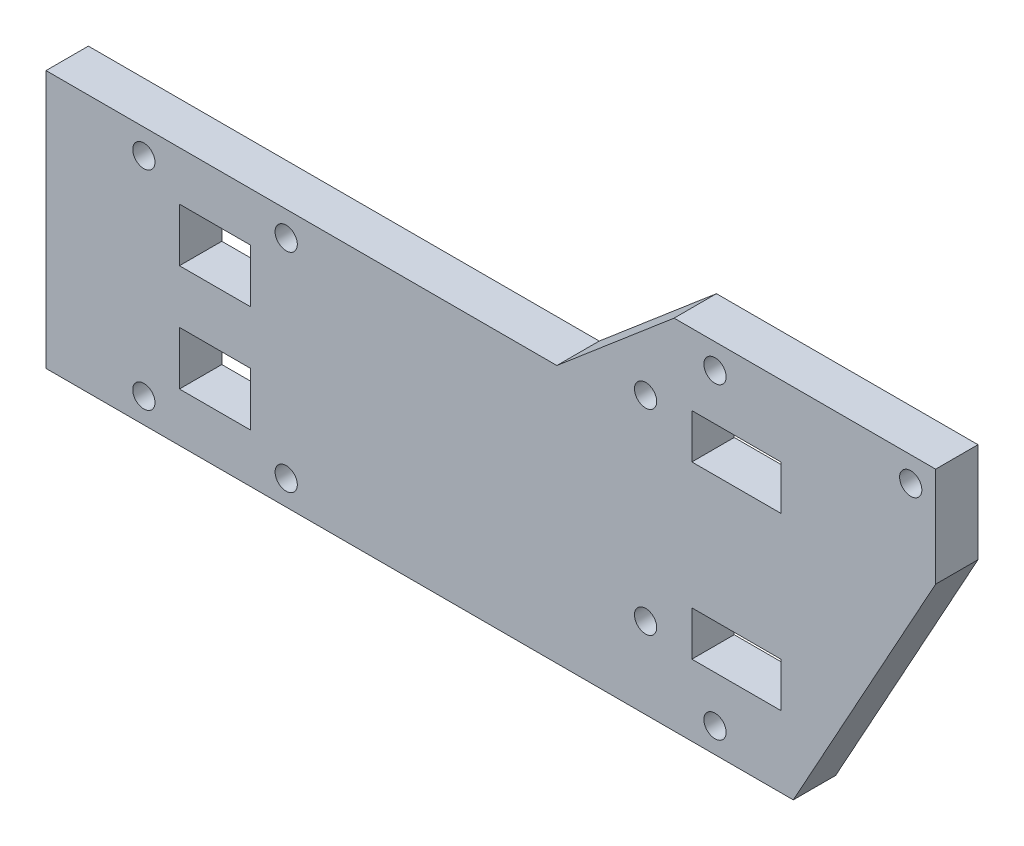
SolidWorks part; units mm, degrees
ref_plane "Front Plane" through (0, 0, 0) normal (0, 0, 1) x (1, 0, 0)
ref_plane "Top Plane" through (0, 0, 0) normal (0, 1, 0) x (1, 0, 0)
ref_plane "Right Plane" through (0, 0, 0) normal (1, 0, 0) x (0, 0, -1)
sketch "Sketch1" plane through (0, 0, 0) normal (0, 0, 1) x (1, 0, 0)
  line L0 (70.6, 40.2) -> (57.4235, 29)
  line L1 (70.6, 40.2) -> (100, 40.2)
  line L2 (100, 40.2) -> (100, 29)
  line L3 (100, 29) -> (84, 0)
  line L4 (84, 0) -> (0, 0)
  line L5 (57.4235, 29) -> (0, 29)
  line L6 (0, 29) -> (0, 0)
  line L7 (64.6, 35.1) -> (70.6, 35.1) construction
  line L8 (70.6, 35.1) -> (70.6, 40.2) construction
  dimension "D1" = 29.4
  dimension "D2" = 100
  dimension "D3" = 29
  dimension "D4" = 40.2
  dimension "D5" = 16
  dimension "D6" = 6
  dimension "D7" = 5.1
extrude "Boss-Extrude1" add sketch "Sketch1" along normal blind 4.7625
sketch "Sketch2" plane through (0, 0, 4.7625) normal (0, 0, 1) x (1, 0, 0)
  line L0 (100, 29) -> (100, 40.2) construction
  line L1 (72.6, 27.2) -> (82.6, 27.2)
  line L2 (72.6, 27.2) -> (72.6, 32.2)
  line L3 (72.6, 32.2) -> (82.6, 32.2)
  line L4 (82.6, 27.2) -> (82.6, 32.2)
  line L5 (72.6, 27.2) -> (82.6, 32.2) construction
  line L6 (72.6, 32.2) -> (82.6, 27.2) construction
  line L7 (100, 40.2) -> (70.6, 40.2) construction
  line L8 (19, 20.5) -> (19, 8.5) construction
  line L9 (72.6, 13) -> (82.6, 13)
  line L10 (72.6, 13) -> (72.6, 8)
  line L11 (72.6, 8) -> (82.6, 8)
  line L12 (82.6, 13) -> (82.6, 8)
  line L13 (72.6, 13) -> (82.6, 8) construction
  line L14 (72.6, 8) -> (82.6, 13) construction
  line L15 (15, 17.5) -> (23, 17.5)
  line L16 (15, 17.5) -> (15, 23.5)
  line L17 (15, 23.5) -> (23, 23.5)
  line L18 (23, 17.5) -> (23, 23.5)
  line L19 (15, 17.5) -> (23, 23.5) construction
  line L20 (15, 23.5) -> (23, 17.5) construction
  line L21 (15, 5.5) -> (23, 5.5)
  line L22 (15, 5.5) -> (15, 11.5)
  line L23 (15, 11.5) -> (23, 11.5)
  line L24 (23, 5.5) -> (23, 11.5)
  line L25 (15, 5.5) -> (23, 11.5) construction
  line L26 (15, 11.5) -> (23, 5.5) construction
  line L27 (0, 29) -> (0, 0) construction
  line L28 (19, 14.5) -> (0, 14.5) construction
  line L29 (0, 0) -> (84, 0) construction
  line L31 (11, 2.8) -> (27, 2.8) construction
  line L32 (11, 2.8) -> (11, 26.2) construction
  line L33 (11, 26.2) -> (27, 26.2) construction
  line L34 (27, 2.8) -> (27, 26.2) construction
  line L35 (11, 2.8) -> (27, 26.2) construction
  line L36 (11, 26.2) -> (27, 2.8) construction
  circle A0 centre (97.2, 37.4) radius 1.25
  circle A1 centre (75.2, 37.4) radius 1.25
  circle A2 centre (67.4, 31.1) radius 1.25
  circle A3 centre (67.4, 9.1) radius 1.25
  circle A4 centre (75.2, 2.8) radius 1.25
  circle A5 centre (11, 26.2) radius 1.25
  circle A6 centre (27, 26.2) radius 1.25
  circle A7 centre (27, 2.8) radius 1.25
  circle A8 centre (11, 2.8) radius 1.25
  point P0 (77.6, 29.7)
  point P9 (77.6, 10.5)
  point P14 (19, 20.5)
  point P19 (19, 8.5)
  dimension "D13" = 2.5
  dimension "D14" = 1.1
  dimension "D1" = 5
  dimension "D2" = 10
  dimension "D3" = 17.4
  dimension "D4" = 8
  dimension "D5" = 14.2
  dimension "D6" = 15
  dimension "D7" = 6
  dimension "D8" = 6
  dimension "D9" = 8
  dimension "D10" = 22
  dimension "D11" = 2.8
  dimension "D12" = 2.8
  dimension "D15" = 5.2
  dimension "D16" = 1.1
  dimension "D17" = 2.8
  dimension "D18" = 16
  dimension "D19" = 2.8
extrude "Cut-Extrude1" cut sketch "Sketch2" against normal through all
sketch "Sketch3" plane through (0, 0, 4.7625) normal (0, 0, 1) x (1, 0, 0)
  line L0 (15, 23.5) -> (23, 23.5) construction
  line L1 (23, 23.5) -> (23, 17.5) construction
  line L2 (23, 17.5) -> (15, 17.5) construction
  line L3 (15, 17.5) -> (15, 23.5) construction
  line L4 (23, 17.5) -> (23, 23.5) construction
  line L5 (15, 17.5) -> (23, 17.5) construction
  line L6 (15, 23.5) -> (15, 17.5) construction
  line L7 (0, 29) -> (0, 0)
  line L8 (0, 0) -> (84, 0)
  line L9 (84, 0) -> (100, 29)
  line L10 (100, 29) -> (100, 40.2)
  line L11 (100, 40.2) -> (70.6, 40.2)
  line L12 (70.6, 40.2) -> (57.4235, 29)
  line L13 (57.4235, 29) -> (0, 29)
  line L14 (0, 29) -> (0, 0)
  line L15 (0, 0) -> (84, 0)
  line L16 (84, 0) -> (100, 29)
  line L17 (100, 29) -> (100, 40.2)
  line L18 (100, 40.2) -> (70.6, 40.2)
  line L19 (70.6, 40.2) -> (57.4235, 29)
  line L20 (57.4235, 29) -> (0, 29)
  line L21 (15, 11.5) -> (23, 11.5) construction
  line L22 (23, 11.5) -> (23, 5.5) construction
  line L23 (23, 5.5) -> (15, 5.5) construction
  line L24 (15, 5.5) -> (15, 11.5) construction
  line L25 (72.6, 13) -> (82.6, 13) construction
  line L26 (82.6, 13) -> (82.6, 8) construction
  line L27 (82.6, 8) -> (72.6, 8) construction
  line L28 (72.6, 8) -> (72.6, 13) construction
  line L29 (72.6, 32.2) -> (82.6, 32.2) construction
  line L30 (82.6, 32.2) -> (82.6, 27.2) construction
  line L31 (82.6, 27.2) -> (72.6, 27.2) construction
  line L32 (72.6, 27.2) -> (72.6, 32.2) construction
  line L33 (15, 23.5) -> (23, 23.5)
  line L34 (23, 23.5) -> (23, 17.5)
  line L35 (23, 17.5) -> (15, 17.5)
  line L36 (15, 17.5) -> (15, 23.5)
  line L37 (23, 17.5) -> (23, 23.5)
  line L38 (15, 17.5) -> (23, 17.5)
  line L39 (15, 23.5) -> (15, 17.5)
  line L40 (15, 11.5) -> (23, 11.5)
  line L41 (23, 11.5) -> (23, 5.5)
  line L42 (23, 5.5) -> (15, 5.5)
  line L43 (15, 5.5) -> (15, 11.5)
  line L44 (72.6, 13) -> (82.6, 13)
  line L45 (82.6, 13) -> (82.6, 8)
  line L46 (82.6, 8) -> (72.6, 8)
  line L47 (72.6, 8) -> (72.6, 13)
  line L48 (72.6, 32.2) -> (82.6, 32.2)
  line L49 (82.6, 32.2) -> (82.6, 27.2)
  line L50 (82.6, 27.2) -> (72.6, 27.2)
  line L51 (72.6, 27.2) -> (72.6, 32.2)
  circle A0 centre (11, 26.2) radius 1.25 construction
  circle A1 centre (27, 26.2) radius 1.25 construction
  circle A2 centre (11, 2.8) radius 1.25 construction
  circle A3 centre (27, 2.8) radius 1.25 construction
  circle A4 centre (67.4, 31.1) radius 1.25 construction
  circle A5 centre (75.2, 37.4) radius 1.25 construction
  circle A6 centre (97.2, 37.4) radius 1.25 construction
  circle A7 centre (67.4, 9.1) radius 1.25 construction
  circle A8 centre (75.2, 2.8) radius 1.25 construction
  circle A9 centre (11, 26.2) radius 1.25
  circle A10 centre (27, 26.2) radius 1.25
  circle A11 centre (11, 2.8) radius 1.25
  circle A12 centre (27, 2.8) radius 1.25
  circle A13 centre (67.4, 31.1) radius 1.25
  circle A14 centre (75.2, 37.4) radius 1.25
  circle A15 centre (97.2, 37.4) radius 1.25
  circle A16 centre (67.4, 9.1) radius 1.25
  circle A17 centre (75.2, 2.8) radius 1.25
  dimension "D1" = 0
